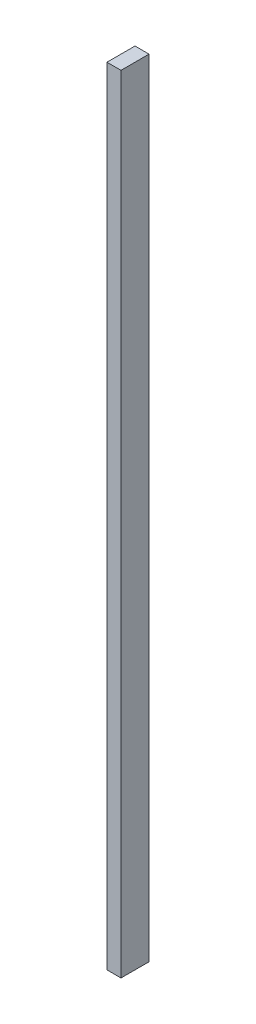
SolidWorks part; units mm, degrees
ref_plane "Front Plane" through (0, 0, 0) normal (0, 0, 1) x (1, 0, 0)
ref_plane "Top Plane" through (0, 0, 0) normal (0, 1, 0) x (1, 0, 0)
ref_plane "Right Plane" through (0, 0, 0) normal (1, 0, 0) x (0, 0, -1)
sketch "Sketch2" plane through (0, 0, 0) normal (0, -1, 0) x (-1, 0, 0)
  line L9 (0, 2) -> (-1, 2)
  line L10 (0, 2) -> (0, 0)
  line L11 (0, 0) -> (-1, 0)
  line L12 (-1, 2) -> (-1, 0)
extrude "Boss-Extrude2" add sketch "Sketch2" against normal blind 56
